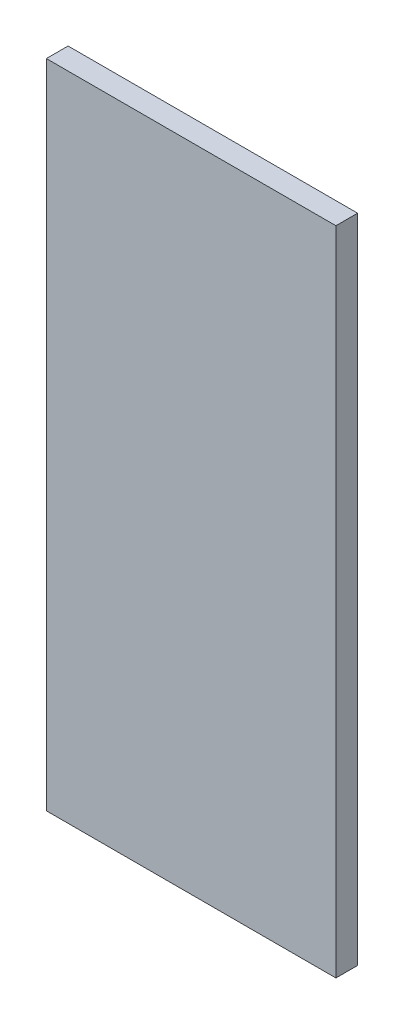
SolidWorks part; units mm, degrees
ref_plane "Plan de face" through (0, 0, 0) normal (0, 0, 1) x (1, 0, 0)
ref_plane "Plan de dessus" through (0, 0, 0) normal (0, 1, 0) x (1, 0, 0)
ref_plane "Plan de droite" through (0, 0, 0) normal (1, 0, 0) x (0, 0, -1)
sketch "Esquisse1" plane through (0, 0, 0) normal (0, 0, 1) x (1, 0, 0)
  line L1 (0, 0) -> (40, 0)
  line L2 (0, 0) -> (0, -90)
  line L3 (0, -90) -> (40, -90)
  line L4 (40, 0) -> (40, -90)
  dimension "D1" = 40
  dimension "D2" = 90
extrude "Boss.-Extru.1" add sketch "Esquisse1" along normal blind 3
